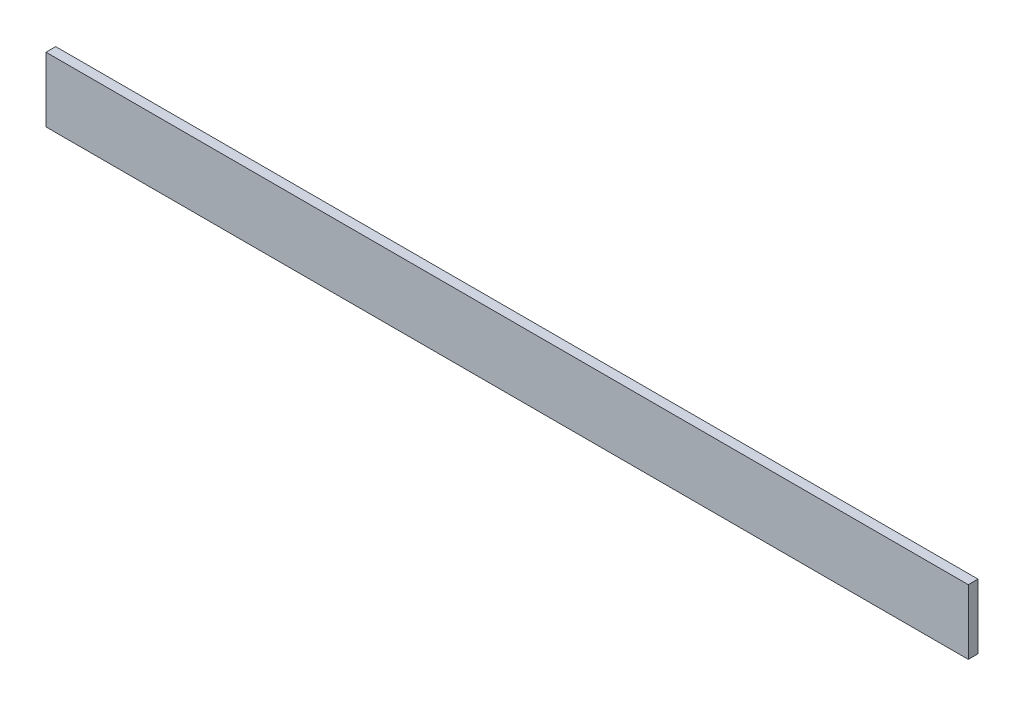
SolidWorks part; units mm, degrees
ref_plane "Front Plane" through (0, 0, 0) normal (0, 0, 1) x (1, 0, 0)
ref_plane "Top Plane" through (0, 0, 0) normal (0, 1, 0) x (1, 0, 0)
ref_plane "Right Plane" through (0, 0, 0) normal (1, 0, 0) x (0, 0, -1)
sketch "Sketch1" plane through (0, 0, -67.5) normal (0, 0, -1) x (-1, 0, 0)
  line L1 (-142.5, 23) -> (142.5, 23)
  line L2 (-142.5, 23) -> (-142.5, 3)
  line L3 (-142.5, 3) -> (142.5, 3)
  line L4 (142.5, 23) -> (142.5, 3)
extrude "Boss-Extrude1" add sketch "Sketch1" along normal blind 3
